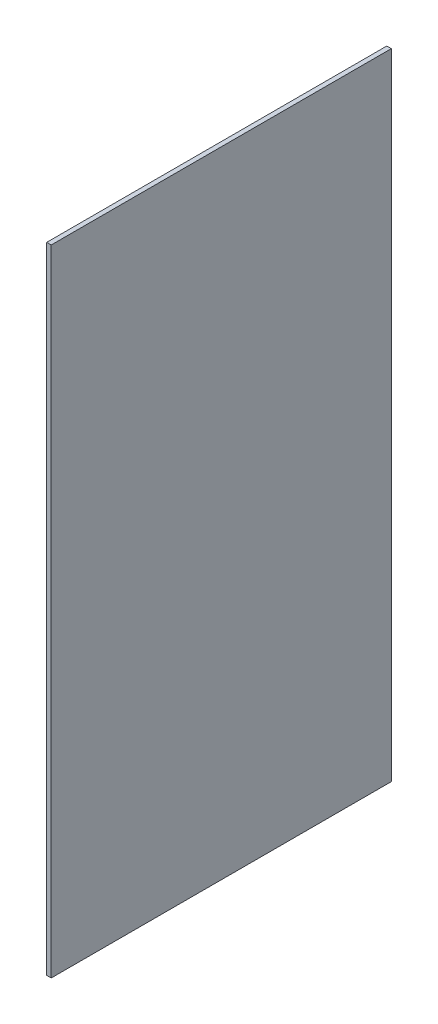
SolidWorks part; units mm, degrees
material "Stainless Steel (ferritic)"
ref_plane "Front Plane" through (0, 0, 0) normal (0, 0, 1) x (1, 0, 0)
ref_plane "Top Plane" through (0, 0, 0) normal (0, 1, 0) x (1, 0, 0)
ref_plane "Right Plane" through (0, 0, 0) normal (1, 0, 0) x (0, 0, -1)
sketch "Sketch1" plane through (0, 0, 0) normal (1, 0, 0) x (0, 0, -1)
  line L1 (15, -28) -> (-15, -28)
  line L2 (15, -28) -> (15, 28)
  line L3 (15, 28) -> (-15, 28)
  line L4 (-15, -28) -> (-15, 28)
  line L5 (15, -28) -> (-15, 28) construction
  line L6 (15, 28) -> (-15, -28) construction
  point P0 (0, 0)
  dimension "D1" = 56
  dimension "D2" = 30
extrude "Boss-Extrude1" add sketch "Sketch1" along normal blind 0.4
